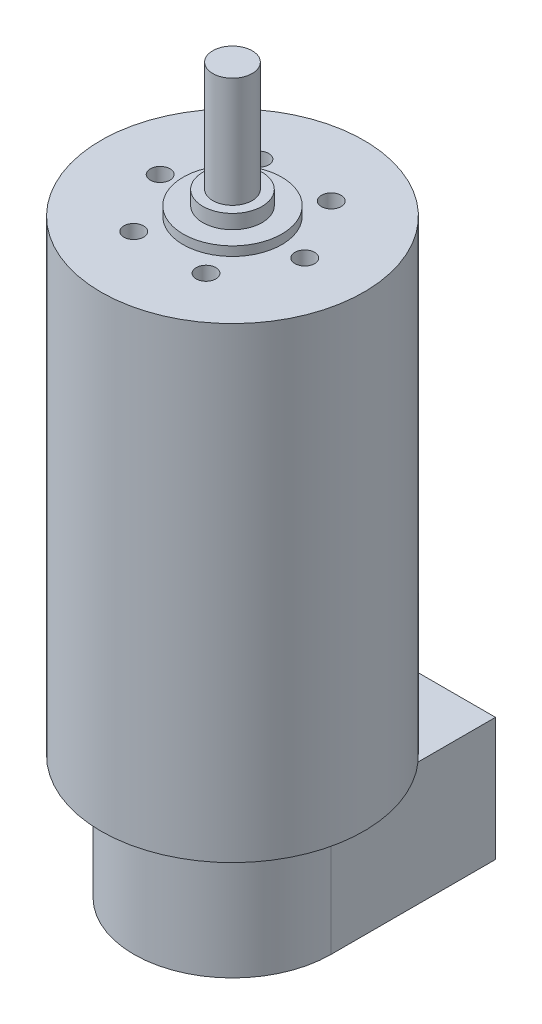
SolidWorks part; units mm, degrees
ref_plane "Front Plane" through (0, 0, 0) normal (0, 0, 1) x (1, 0, 0)
ref_plane "Top Plane" through (0, 0, 0) normal (0, 1, 0) x (1, 0, 0)
ref_plane "Right Plane" through (0, 0, 0) normal (1, 0, 0) x (0, 0, -1)
sketch "Sketch1" plane through (0, 0, 0) normal (0, 1, 0) x (1, 0, 0)
  circle A0 centre (0, 0) radius 20
  dimension "D1" = 40
extrude "Boss-Extrude1" add sketch "Sketch1" along normal blind 71
sketch "Sketch2" plane through (0, 71, 0) normal (0, 1, 0) x (1, 0, 0)
  circle A0 centre (0, 0) radius 7.5
  dimension "D1" = 15
extrude "Boss-Extrude2" add sketch "Sketch2" along normal blind 1.4
sketch "Sketch3" plane through (0, 72.4, 0) normal (0, 1, 0) x (1, 0, 0)
  circle A0 centre (0, 0) radius 4.5
  dimension "D1" = 9
extrude "Boss-Extrude3" add sketch "Sketch3" along normal blind 2.15
sketch "Sketch4" plane through (0, 74.55, 0) normal (0, 1, 0) x (1, 0, 0)
  circle A0 centre (0, 0) radius 3
  dimension "D1" = 6
extrude "Boss-Extrude4" add sketch "Sketch4" along normal blind 16.75
sketch "Sketch5" plane through (0, 71, 0) normal (0, 1, 0) x (1, 0, 0)
  circle A1 centre (-11, 0) radius 1.5
  dimension "D2" = 11
  dimension "D3" = 3
  dimension "D1" = 0
extrude "Cut-Extrude1" cut sketch "Sketch5" against normal blind 5
pattern_circular "CirPattern1" count 6 over 360 about axis through (0, 0, 0) along (0, 1, 0) of "Cut-Extrude1"
sketch "Sketch6" plane through (0, 0, 0) normal (0, -1, 0) x (-1, 0, 0)
  line L0 (15, 0) -> (15, 25)
  line L1 (-15, 0) -> (-15, 25)
  line L2 (15, 25) -> (-15, 25)
  arc A0 (-15, 0) -> (15, 0) centre (0, 0) ccw
  dimension "D1" = 30
  dimension "D2" = 25
extrude "Boss-Extrude5" add sketch "Sketch6" along normal blind 18.73
